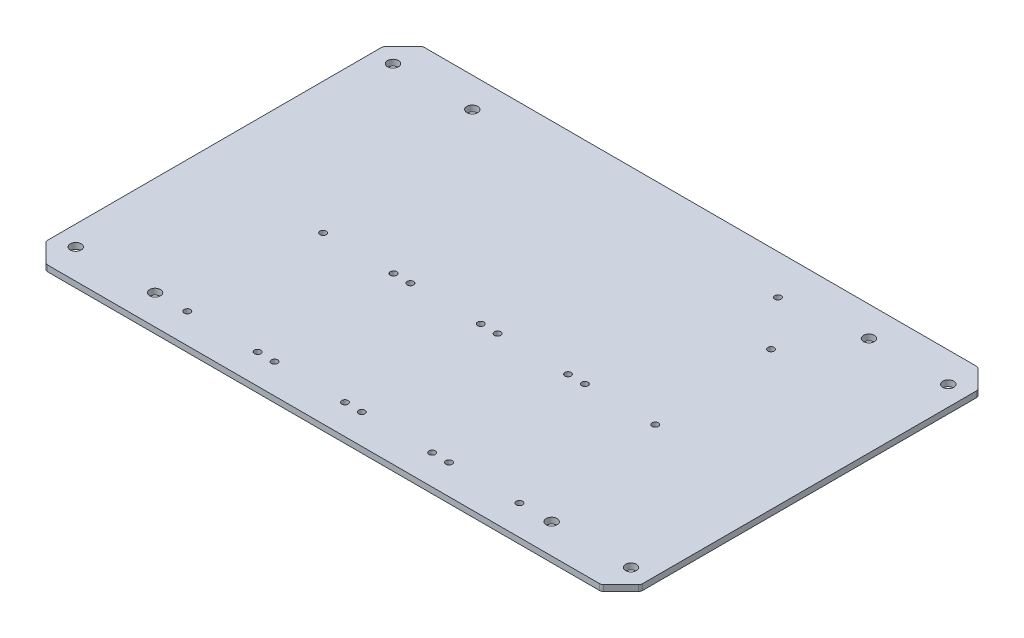
SolidWorks part; units mm, degrees
ref_plane "Plan de face" through (0, 0, 0) normal (0, 0, 1) x (1, 0, 0)
ref_plane "Plan de dessus" through (0, 0, 0) normal (0, 1, 0) x (1, 0, 0)
ref_plane "Plan de droite" through (0, 0, 0) normal (1, 0, 0) x (0, 0, -1)
sketch "Esquisse1" plane through (0, 0, 0) normal (0, 1, 0) x (1, 0, 0)
  line L1 (-150, -95) -> (150, -95)
  line L2 (-150, -95) -> (-150, 95)
  line L3 (-150, 95) -> (150, 95)
  line L4 (150, -95) -> (150, 95)
  line L5 (-150, -95) -> (150, 95) construction
  line L6 (-150, 95) -> (150, -95) construction
  point P0 (0, 0)
  dimension "D1" = 300
  dimension "D2" = 190
extrude "Boss.-Extru.1" add sketch "Esquisse1" along normal blind 3
chamfer "Chanfrein1" distance 10 angle 45 4 edges at (-150, 1.5, 95) (150, 1.5, 95) (150, 1.5, -95) (-150, 1.5, -95)
fillet "Congé1" radius 2 8 edges at (-150, 1.5, -85) (-140, 1.5, -95) (140, 1.5, -95) (150, 1.5, -85) (150, 1.5, 85) (140, 1.5, 95) (-140, 1.5, 95) (-150, 1.5, 85)
sketch "Esquisse2" plane through (0, 0, 0) normal (0, -1, 0) x (1, 0, 0)
  line L0 (-140, 80) -> (-100, 80) construction
  line L3 (-150, -84.1716) -> (-150, 84.1716) construction
  line L4 (-139.1716, 95) -> (139.1716, 95) construction
  circle A0 centre (-140, 80) radius 2.75
  circle A1 centre (-100, 80) radius 2.75
  point P4 (-120, 80)
  point P5 (0, 0)
  point P9 (0, 0)
  dimension "D1" = 5.5
  dimension "D2" = 40
  dimension "D3" = 10
  dimension "D4" = 15
extrude "Enlèv. mat.-Extru.1" cut sketch "Esquisse2" against normal through all
pattern_linear "Répétition linéaire1" count 2 spacing 240 along (1, 0, 0) count 2 spacing 160 along (0, 0, -1) of "Enlèv. mat.-Extru.1"
sketch "Esquisse3" plane through (0, 3, 0) normal (0, 1, 0) x (1, 0, 0)
  line L0 (-100, -80) -> (85, -80) construction
  line L1 (0, 0) -> (0, 50000) construction
  line L2 (0, 0) -> (50000, 0) construction
  circle A0 centre (-83.75, -80) radius 1.6
  circle A1 centre (-48.25, -80) radius 1.6
  circle A2 centre (-83.75, -11.5) radius 1.6
  circle A3 centre (-48.25, -11.5) radius 1.6
  dimension "D1" = 3.2
  dimension "D2" = 35.5
  dimension "D3" = 16.25
  dimension "D4" = 68.5
extrude "Enlèv. mat.-Extru.2" cut sketch "Esquisse3" against normal through all
pattern_linear "Répétition linéaire2" count 4 spacing 44 along (1, 0, 0) of "Enlèv. mat.-Extru.2"
sketch "Esquisse4" plane through (0, 3, 0) normal (0, 1, 0) x (1, 0, 0)
  circle A0 centre (59.1, 75) radius 1.6
  circle A1 centre (80, 50.6) radius 1.6
  circle A2 centre (100, 80) radius 2.75 construction
  circle A3 centre (100, 80) radius 2.75
  point P7 (0, 0)
  dimension "D1" = 3.2
  dimension "D4" = 20
  dimension "D2" = 24.4
  dimension "D3" = 20.9
  dimension "D5" = 5
extrude "Enlèv. mat.-Extru.3" cut sketch "Esquisse4" against normal blind 10
